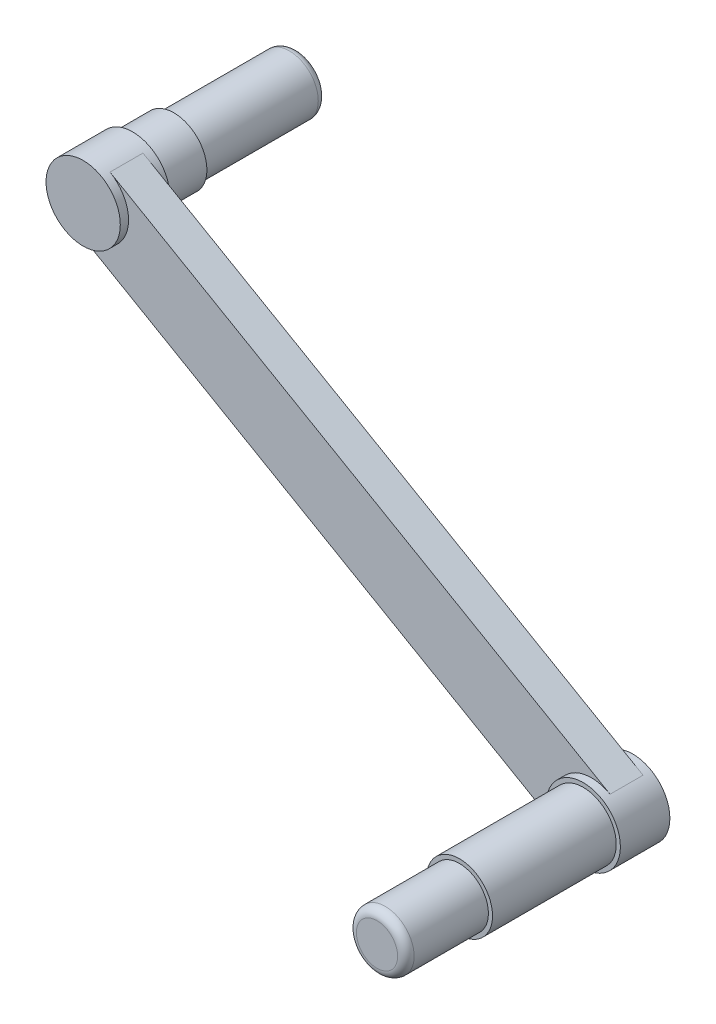
SolidWorks part; units mm, degrees
ref_plane "Front Plane" through (0, 0, 0) normal (0, 0, 1) x (1, 0, 0)
ref_plane "Top Plane" through (0, 0, 0) normal (0, 1, 0) x (1, 0, 0)
ref_plane "Right Plane" through (0, 0, 0) normal (1, 0, 0) x (0, 0, -1)
sketch "Sketch1" plane through (0, 0, 0) normal (0, 0, 1) x (1, 0, 0)
  circle A0 centre (0, 0) radius 3.5
  dimension "D1" = 7
extrude "Boss-Extrude1" add sketch "Sketch1" against normal blind 15 contours A0
sketch "Sketch2" plane through (0, 0, 0) normal (0, 0, 1) x (1, 0, 0)
  circle A0 centre (0, 0) radius 4
  dimension "D1" = 8
extrude "Boss-Extrude2" add sketch "Sketch2" along normal blind 5 contours A0
sketch "Sketch3" plane through (0, 0, 5) normal (0, 0, 1) x (1, 0, 0)
  circle A0 centre (0, 0) radius 4.5
  dimension "D1" = 9
extrude "Boss-Extrude3" add sketch "Sketch3" along normal blind 5 contours A0
sketch "Sketch5" plane through (0, 0, 10) normal (0, 0, 1) x (1, 0, 0)
  line L0 (0, 0) -> (60.6218, -35) construction
  line L1 (0, 0.7947) -> (0, -0.8392)
  line L2 (-2.25, -3.8971) -> (2.25, 3.8971)
  line L3 (2.25, 3.8971) -> (62.8718, -31.1029)
  line L4 (-2.25, -3.8971) -> (58.3718, -38.8971)
  circle A0 centre (60.6218, -35) radius 4.5
  circle A2 centre (0, 0) radius 4.5 construction
  dimension "D2" = 9
  dimension "D1" = 60
  dimension "D3" = 90
  dimension "D4" = 70
extrude "Boss-Extrude4" add sketch "Sketch5" against normal blind 4
sketch "Sketch6" plane through (0, 0, 10) normal (0, 0, 1) x (1, 0, 0)
  circle A0 centre (0, 0) radius 4.5
  circle A1 centre (60.6218, -35) radius 4.5
  dimension "D1" = 9
  dimension "D2" = 9
extrude "Boss-Extrude5" add sketch "Sketch6" along normal blind 1 and the other way blind 5
sketch "Sketch7" plane through (0, 0, 11) normal (0, 0, 1) x (1, 0, 0)
  circle A0 centre (60.6218, -35) radius 4
  dimension "D1" = 8
extrude "Boss-Extrude6" add sketch "Sketch7" along normal blind 15
sketch "Sketch8" plane through (0, 0, 26) normal (0, 0, 1) x (1, 0, 0)
  circle A0 centre (60.6218, -35) radius 3.5
  dimension "D1" = 7
extrude "Boss-Extrude7" add sketch "Sketch8" along normal blind 10
fillet "Fillet3" radius 1 2 edges at (64.1218, -35, 36) (3.5, 0, -15)
